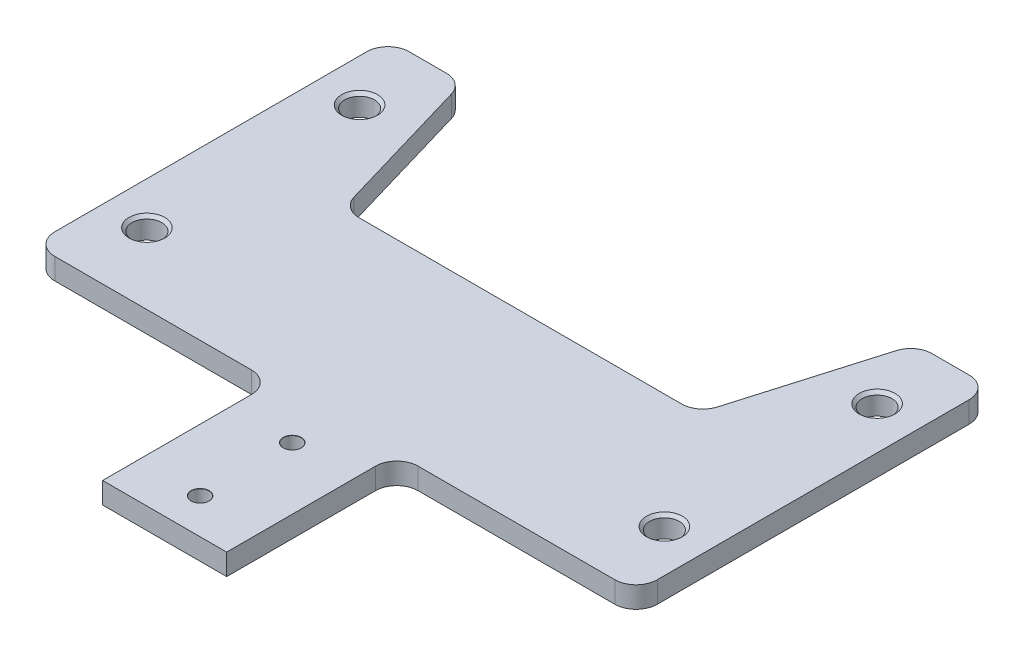
SolidWorks part; units mm, degrees
ref_plane "Front Plane" through (0, 0, 0) normal (0, 0, 1) x (1, 0, 0)
ref_plane "Top Plane" through (0, 0, 0) normal (0, 1, 0) x (1, 0, 0)
ref_plane "Right Plane" through (0, 0, 0) normal (1, 0, 0) x (0, 0, -1)
sketch "Sketch2" plane through (0, 0, 0) normal (0, 1, 0) x (1, 0, 0)
  line L1 (42.5, 0) -> (42.5, 50)
  line L2 (42.5, 50) -> (22.5, 50)
  line L3 (22.5, 50) -> (8.75, 26.1843)
  line L4 (8.75, 26.1843) -> (-8.75, 26.1843)
  line L5 (-8.75, 26.1843) -> (-22.5, 50)
  line L6 (-22.5, 50) -> (-42.5, 50)
  line L7 (-42.5, 50) -> (-42.5, 0)
  line L9 (-42.5, 0) -> (42.5, 0)
  point P0 (0, 26.1843)
  point P3 (0, 0)
  point P11 (32.5, 50)
  point P13 (-32.5, 50)
  dimension "D1" = 17.5
  dimension "D2" = 85
  dimension "D3" = 50
  dimension "D4" = 60
  dimension "D5" = 60
  dimension "D6" = 20
extrude "Boss-Extrude1" add sketch "Sketch2" along normal blind 3
sketch "Sketch3" plane through (0, 0, -26.1843) normal (0, 0, -1) x (-1, 0, 0)
  line L6 (-8.75, 0) -> (8.75, 0)
  line L7 (-8.75, 0) -> (-8.75, 1)
  line L8 (-8.75, 1) -> (8.75, 1)
  line L9 (8.75, 0) -> (8.75, 1)
  point P5 (0, 0)
  dimension "D1" = 17.5
  dimension "D2" = 1
extrude "Cut-Extrude1" [suppressed] cut sketch "Sketch3" against normal through all
sketch "Sketch10" plane through (0, 3, 0) normal (0, 1, 0) x (1, 0, 0)
  line L0 (-8.75, 0) -> (-8.75, -24)
  line L1 (-42.5, 0) -> (42.5, 0) construction
  line L2 (-8.75, -24) -> (8.75, -24)
  line L3 (8.75, -24) -> (8.75, 0)
  line L4 (8.75, 0) -> (-8.75, 0)
  point P4 (0, 0)
  dimension "D1" = 17.5
  dimension "D2" = 24
extrude "Boss-Extrude2" add sketch "Sketch10" against normal up to surface (3 mm away) up to face at (0, 0, -31.5461)
hole_wizard "Ø2.5 (2.5) Diameter Hole1" positions "Sketch4" profile "Sketch5" hole size "Ø2.5" standard "ANSI Metric"
sketch "Sketch4" plane through (0, 3, 0) normal (0, 1, 0) x (1, 0, 0)
  line L4 (-8.75, -24) -> (8.75, -24) construction
  point P0 (0, -19)
  point P2 (0, -6)
  dimension "D1" = 13
  dimension "D2" = 5
  dimension "D3" = 8.75
sketch "Sketch5" plane through (0, 3, 19) normal (1, 0, 0) x (0, 0, 1)
  line L0 (0, 0) -> (0, 7.1011)
  line L1 (0, 7.1011) -> (1.25, 6.35)
  line L2 (1.25, 6.35) -> (1.25, 0.025)
  line L3 (1.25, 0.025) -> (1.275, 0)
  line L5 (1.275, 0) -> (0, 0)
  line L6 (-1.25, 0.025) -> (-1.275, 0) construction
  line L10 (0, 7.1011) -> (-1.25, 6.35) construction
  line L11 (0, -6.35) -> (0, 107.95) construction
  dimension "Hole Dia." = 2.5
  dimension "Hole Depth" = 6.35
  dimension "Near C'Sink Dia." = 2.55
  dimension "Near C'Sink Angle" = 90
  dimension "Drill Angle" = 118
hole_wizard "M5x0.8 Tapped Hole1" positions "Sketch6" profile "Sketch7" tap size "M5x0.8" standard "ANSI Metric"
sketch "Sketch6" plane through (0, 3, 0) normal (0, 1, 0) x (1, 0, 0)
  line L1 (-22.5, 50) -> (-42.5, 50) construction
  line L2 (42.5, 50) -> (22.5, 50) construction
  line L3 (42.5, 0) -> (42.5, 50) construction
  line L4 (-42.5, 50) -> (-42.5, 0) construction
  line L5 (-42.5, 0) -> (-8.75, 0) construction
  point P0 (-36.5, 40)
  point P2 (36.5, 40)
  point P18 (-36.5, 10)
  point P20 (36.5, 10)
  dimension "D1" = 6
  dimension "D2" = 10
  dimension "D3" = 10
  dimension "D4" = 6
  dimension "D5" = 10
  dimension "D6" = 10
sketch "Sketch7" plane through (-36.5, 3, -40) normal (1, 0, 0) x (0, 0, 1)
  line L0 (0, 0) -> (0, 13.6618)
  line L1 (0, 13.6618) -> (2.1, 12.4)
  line L2 (2.1, 12.4) -> (2.1, 0.425)
  line L3 (2.1, 0.425) -> (2.525, 0)
  line L5 (2.525, 0) -> (0, 0)
  line L6 (-2.1, 0.425) -> (-2.525, 0) construction
  line L10 (0, 13.6618) -> (-2.1, 12.4) construction
  line L11 (0, -6.35) -> (0, 107.95) construction
  dimension "Tap Drill Dia." = 4.2
  dimension "Tap Drill Depth" = 12.4
  dimension "Near C'Sink Dia." = 5.05
  dimension "Near C'Sink Angle" = 90
  dimension "Drill Angle" = 118
cosmetic thread "Hole Thread3" parameters "D1"=10, "D2"=5
cosmetic thread "Hole Thread4" parameters "D1"=10, "D2"=5
cosmetic thread "Hole Thread5" parameters "D1"=10, "D2"=5
cosmetic thread "Hole Thread6" parameters "D1"=10, "D2"=5
sketch "Sketch8" plane through (0, 0, -26.1843) normal (0, 0, -1) x (-1, 0, 0)
  line L5 (-8.75, 3) -> (-8.75, 0) construction
  line L6 (-13, 0) -> (-8.75, 0)
  line L7 (-13, 0) -> (-13, 1.3)
  line L8 (-13, 1.3) -> (-8.75, 1.3)
  line L9 (-8.75, 0) -> (-8.75, 1.3)
  line L10 (0, 0) -> (0, 12.6228) construction
  line L11 (8.75, 0) -> (8.75, 1.3)
  line L12 (13, 1.3) -> (8.75, 1.3)
  line L13 (13, 0) -> (13, 1.3)
  line L14 (13, 0) -> (8.75, 0)
  line L15 (-22.5, 0) -> (-8.75, 0) construction
  dimension "D1" = 4.25
  dimension "D2" = 1.3
extrude "Cut-Extrude2" [suppressed] cut sketch "Sketch8" against normal through all both and the other way through all
sketch "Sketch9" plane through (0, 0, 0) normal (0, -1, 0) x (1, 0, 0)
  line L0 (-32, -50) -> (-25, -26.1843)
  line L1 (-22.5, -50) -> (-42.5, -50) construction
  line L3 (25, -26.1843) -> (32, -50)
  line L4 (42.5, -50) -> (22.5, -50) construction
  line L5 (32, -50) -> (-32, -50)
  line L6 (-25, -26.1843) -> (25, -26.1843)
  line L7 (8.75, -26.1843) -> (-8.75, -26.1843) construction
  point P8 (0, -50)
  point P12 (0, -26.1843)
  dimension "D1" = 64
  dimension "D2" = 50
extrude "Cut-Extrude3" cut sketch "Sketch9" against normal through all
fillet "Fillet1" radius 3 10 edges at (42.5, 1.5, -50) (-42.5, 1.5, -50) (-32, 1.5, -50) (32, 1.5, -50) (25, 1.5, -26.1843) (-25, 1.5, -26.1843) (42.5, 1.5, 0) (-42.5, 1.5, 0) (8.75, 1.5, 0) (-8.75, 1.5, 0)
fillet "Fillet2" [suppressed] radius 1
